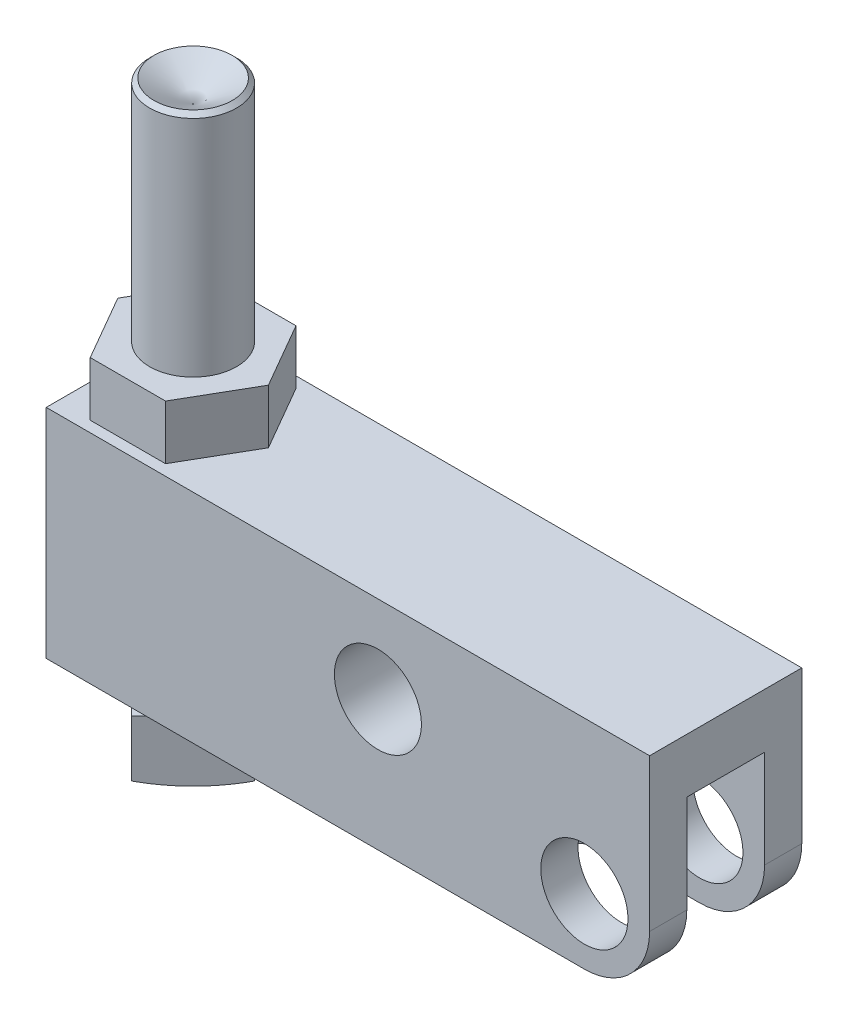
SolidWorks part; units mm, degrees
material "Alloy Steel"
ref_plane "Front Plane" through (0, 0, 0) normal (0, 0, 1) x (1, 0, 0)
ref_plane "Top Plane" through (0, 0, 0) normal (0, 1, 0) x (1, 0, 0)
ref_plane "Right Plane" through (0, 0, 0) normal (1, 0, 0) x (0, 0, -1)
sketch "Sketch11" plane through (0, 0, 0) normal (0, 0, 1) x (1, 0, 0)
  line L1 (-78.5876, 22.225) -> (9.525, 22.225)
  line L2 (-78.5876, 22.225) -> (-78.5876, -9.525)
  line L3 (-78.5876, -9.525) -> (9.525, -9.525)
  line L4 (9.525, 22.225) -> (9.525, -9.525)
  circle A0 centre (0, 0) radius 6.369
  circle A1 centre (-30.1498, 9.525) radius 6.3563
  dimension "D1" = 12.7381
  dimension "D6" = 12.7127
  dimension "D2" = 9.525
  dimension "D3" = 78.5876
  dimension "D4" = 31.75
  dimension "D5" = 30.1498
  dimension "D7" = 9.525
  dimension "D8" = 9.525
extrude "Extrude3" add sketch "Sketch11" along normal mid plane 22.225
sketch "Sketch12" plane through (0, -9.525, 0) normal (0, -1, 0) x (1, 0, 0)
  line L0 (0, 0) -> (-16.2248, 0) construction
  line L1 (-12.7127, 5.6769) -> (9.525, 5.6769)
  line L2 (9.525, 11.1125) -> (9.525, -11.1125) construction
  line L3 (9.525, 5.6769) -> (9.525, -5.6769)
  line L4 (-78.5876, 11.1125) -> (9.525, 11.1125) construction
  line L5 (-12.7127, -5.6769) -> (9.525, -5.6769)
  arc A0 (-12.7127, 5.6769) -> (-12.7127, -5.6769) centre (-12.7127, 0) ccw
  dimension "D3" = 27.9146
  dimension "D1" = 11.3538
  dimension "D2" = 5.4356
extrude "Cut-Extrude1" cut sketch "Sketch12" against normal blind 23.7998
fillet "Fillet1" radius 9.525 2 edges at (9.525, -9.525, -8.3947) (9.525, -9.525, 8.3947)
sketch "Sketch13" plane through (0, 22.225, 0) normal (0, 1, 0) x (1, 0, 0)
  line L1 (-57.2513, 0) -> (-62.7505, 9.525)
  line L2 (-62.7505, 9.525) -> (-73.7491, 9.525)
  line L3 (-73.7491, 9.525) -> (-79.2483, 0)
  line L4 (-79.2483, 0) -> (-73.7491, -9.525)
  line L5 (-73.7491, -9.525) -> (-62.7505, -9.525)
  line L6 (-62.7505, -9.525) -> (-57.2513, 0)
  circle A0 centre (-68.2498, 0) radius 9.525 construction
  dimension "D1" = 19.05
  dimension "D2" = 68.2498
extrude "Extrude4" add sketch "Sketch13" along normal blind 7.9248
sketch "Sketch14" plane through (0, 0, 0) normal (0, 0, 1) x (1, 0, 0)
  line L0 (-68.2498, 26.5852) -> (-68.2498, -12.9942) construction
  line L1 (-57.2513, 30.1498) -> (-57.2513, 22.225) construction
  line L2 (-79.2483, 30.1498) -> (-79.2483, 22.225) construction
  line L3 (-68.2498, 60.2004) -> (-73.9648, 63.5)
  line L4 (-73.9648, 63.5) -> (-74.5998, 62.865)
  line L5 (-74.5998, 62.865) -> (-74.5998, -12.7)
  line L6 (-74.5998, -12.7) -> (-90.1509, -12.7)
  line L7 (-90.1509, -12.7) -> (-90.1509, -13.462)
  line L9 (-68.2498, 60.2004) -> (-68.2498, -22.225)
  line L10 (-78.5876, -9.525) -> (0, -9.525) construction
  arc A0 (-90.1509, -13.462) -> (-68.2498, -22.225) centre (-68.2498, 9.525) ccw
  dimension "D5" = 31.75
  dimension "D1" = 60
  dimension "D2" = 11.43
  dimension "D3" = 45
  dimension "D4" = 76.2
  dimension "D6" = 12.7
  dimension "D7" = 9.525
  dimension "D8" = 0.762
  dimension "D9" = 12.7
  dimension "D10" = 68.2498
revolve "Revolve2" add sketch "Sketch14" angle 360 about L0
sketch "Sketch15" plane through (0, -12.7, 0) normal (0, 1, 0) x (1, 0, 0)
  line L0 (-59.2695, 0) -> (-77.2301, 0) construction
  line L1 (-68.2498, 8.9803) -> (-77.2301, 0)
  line L2 (-77.2301, 0) -> (-68.2498, -8.9803)
  line L3 (-68.2498, -8.9803) -> (-59.2695, 0)
  line L4 (-59.2695, 0) -> (-68.2498, 8.9803)
  circle A0 centre (-68.2498, 0) radius 6.35 construction
  circle A1 centre (-68.2498, 0) radius 21.9011 construction
  circle A2 centre (-68.2498, 0) radius 21.9011
  dimension "D1" = 12.7
extrude "Cut-Extrude2" cut sketch "Sketch15" against normal through all
